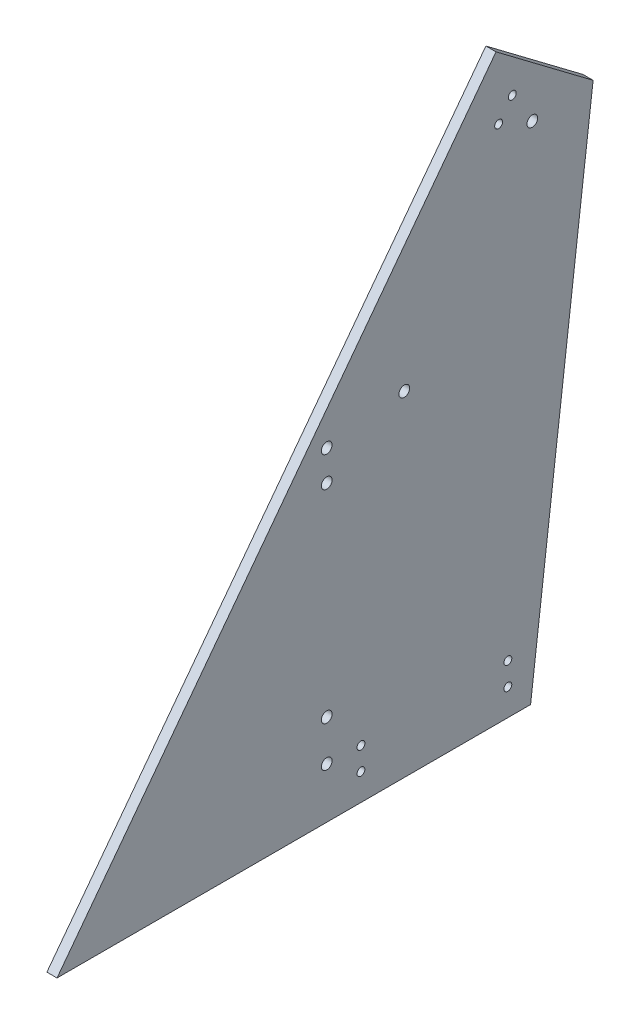
SolidWorks part; units mm, degrees
material "PC High Viscosity"
ref_plane "Front Plane" through (0, 0, 0) normal (0, 0, 1) x (1, 0, 0)
ref_plane "Top Plane" through (0, 0, 0) normal (0, 1, 0) x (1, 0, 0)
ref_plane "Right Plane" through (0, 0, 0) normal (1, 0, 0) x (0, 0, -1)
sketch "Sketch1" plane through (0, 0, 0) normal (1, 0, 0) x (0, 0, -1)
  line L0 (0, 0) -> (275.1498, 365.1362)
  line L2 (336.0059, 319.2779) -> (296.8035, 0)
  line L3 (296.8035, 0) -> (0, 0)
  line L4 (275.1498, 365.1362) -> (336.0059, 319.2779)
  dimension "D1" = 53
  dimension "D2" = 457.2
  dimension "D3" = 76.2
  dimension "D4" = 120
extrude "Boss-Extrude1" add sketch "Sketch1" along normal blind 6.35
sketch "Sketch2" plane through (6.35, 0, 0) normal (1, 0, 0) x (0, 0, -1)
  line L0 (162.6923, 215.9) -> (175.3923, 215.9) construction
  line L3 (275.1498, 365.1362) -> (0, 0) construction
  line L4 (175.3923, 215.9) -> (175.3923, 0) construction
  line L5 (0, 0) -> (296.8035, 0) construction
  circle A0 centre (169.0423, 203.2) radius 3.3655
  circle A1 centre (169.0423, 184.15) radius 3.3655
  circle A2 centre (169.0423, 57.15) radius 3.3655
  circle A3 centre (169.0423, 31.75) radius 3.3655
  point P16 (169.0423, 215.9)
  dimension "D3" = 12.7
  dimension "D7" = 6.731
  dimension "D1" = 215.9
  dimension "D2" = 12.7
  dimension "D4" = 19.05
  dimension "D5" = 158.75
  dimension "D6" = 25.4
  dimension "D8" = 6.35
extrude "Cut-Extrude1" cut sketch "Sketch2" against normal through all
sketch "Sketch3" plane through (6.35, 0, 0) normal (1, 0, 0) x (0, 0, -1)
  line L0 (285.3463, 336.4617) -> (276.7861, 325.1019) construction
  line L1 (275.1498, 365.1362) -> (0, 0) construction
  line L3 (336.0059, 319.2779) -> (275.1498, 365.1362) construction
  line L4 (0, 0) -> (296.8035, 0) construction
  circle A0 centre (190.5, 30.988) radius 2.4638
  circle A1 centre (190.5, 16.764) radius 2.4638
  circle A2 centre (282.575, 30.988) radius 2.4638
  circle A3 centre (282.575, 16.764) radius 2.4638
  circle A4 centre (285.3463, 336.4617) radius 2.4638
  circle A5 centre (276.7861, 325.1019) radius 2.4638
  dimension "D1" = 190.5
  dimension "D3" = 4.9276
  dimension "D2" = 282.575
  dimension "D4" = 25.4
  dimension "D5" = 16.764
  dimension "D6" = 14.224
  dimension "D7" = 16.764
  dimension "D8" = 14.224
extrude "Cut-Extrude2" cut sketch "Sketch3" against normal through all
sketch "Sketch4" plane through (6.35, 0, 0) normal (1, 0, 0) x (0, 0, -1)
  line L0 (275.1498, 365.1362) -> (0, 0) construction
  line L1 (336.0059, 319.2779) -> (275.1498, 365.1362) construction
  circle A0 centre (297.8987, 316.1894) radius 3.3655
  circle A1 centre (217.6467, 209.6913) radius 3.3655
  dimension "D1" = 6.731
  dimension "D2" = 47.625
  dimension "D3" = 47.625
  dimension "D4" = 25.4
  dimension "D5" = 158.75
extrude "Cut-Extrude3" cut sketch "Sketch4" against normal through all
